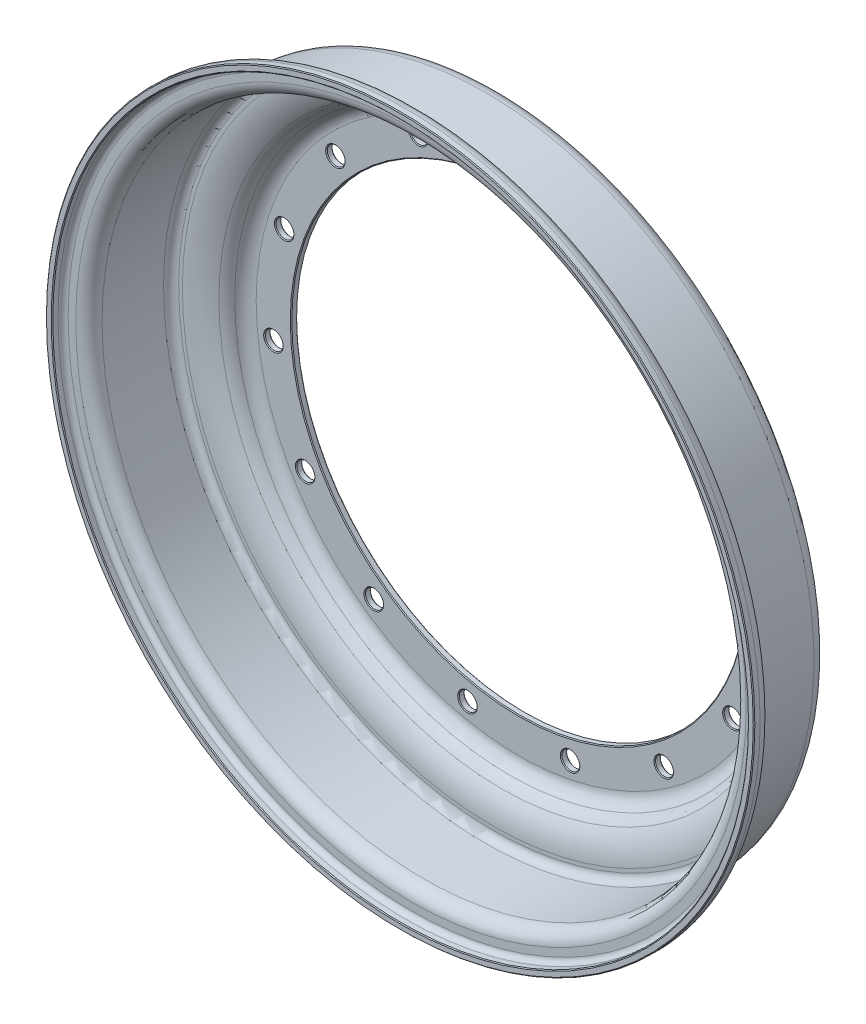
SolidWorks part; units mm, degrees
material "6061-T6 (SS)"
ref_plane "Front Plane" through (0, 0, 0) normal (0, 0, 1) x (1, 0, 0)
ref_plane "Top Plane" through (0, 0, 0) normal (0, 1, 0) x (1, 0, 0)
ref_plane "Right Plane" through (0, 0, 0) normal (1, 0, 0) x (0, 0, -1)
ref_axis "Axis1" through (0, 0, -1.8731) along (0, 0, 1)
sketch "Sketch1" plane through (0, 0, 0) normal (1, 0, 0) x (0, 0, -1)
  line L0 (0, 114.3) -> (0, 131.8108)
  line L1 (-12.8246, 156.0362) -> (-12.8246, 157.8624)
  line L2 (-19.8095, 164.8473) -> (-50.6705, 164.8473)
  line L3 (-54.0991, 168.2759) -> (-54.0991, 172.0859)
  line L4 (-59.8142, 177.801) -> (-62.8622, 177.801)
  line L5 (-3.175, 114.3) -> (-3.175, 131.8108)
  line L6 (-15.9996, 156.0362) -> (-15.9996, 157.8624)
  line L7 (-19.8095, 161.6723) -> (-50.6705, 161.6723)
  line L8 (-57.2741, 168.2759) -> (-57.2741, 172.0859)
  line L9 (-59.8142, 174.626) -> (-62.8622, 174.626)
  line L10 (-62.8622, 177.801) -> (-62.8622, 174.626)
  line L11 (-3.175, 114.3) -> (0, 114.3)
  arc A0 (0, 131.8108) -> (-6.2586, 141.1935) centre (-10.1625, 131.8108) ccw
  arc A1 (-6.2586, 141.1935) -> (-9.1491, 143.604) centre (-3.8185, 147.0578) cw
  arc A2 (-9.1491, 143.604) -> (-12.8246, 156.0362) centre (10.0384, 156.0362) cw
  arc A3 (-12.8246, 157.8624) -> (-19.8095, 164.8473) centre (-19.8095, 157.8624) ccw
  arc A4 (-50.6705, 164.8473) -> (-54.0991, 168.2759) centre (-50.6705, 168.2759) cw
  arc A5 (-54.0991, 172.0859) -> (-59.8142, 177.801) centre (-59.8142, 172.0859) ccw
  arc A6 (-3.175, 131.8108) -> (-7.4782, 138.2621) centre (-10.1625, 131.8108) ccw
  arc A7 (-7.4782, 138.2621) -> (-11.8137, 141.8775) centre (-3.8185, 147.0578) cw
  arc A8 (-11.8137, 141.8775) -> (-15.9996, 156.0362) centre (10.0384, 156.0362) cw
  arc A9 (-15.9996, 157.8624) -> (-19.8095, 161.6723) centre (-19.8095, 157.8624) ccw
  arc A10 (-50.6705, 161.6723) -> (-57.2741, 168.2759) centre (-50.6705, 168.2759) cw
  arc A11 (-57.2741, 172.0859) -> (-59.8142, 174.626) centre (-59.8142, 172.0859) ccw
  dimension "D1" = 114.3
  dimension "D2" = 17.5108
  dimension "D3" = 9.3828
  dimension "D4" = 2.8905
  dimension "D5" = 6.2586
  dimension "D6" = 2.4105
  dimension "D7" = 1.8263
  dimension "D8" = 12.9642
  dimension "D9" = 9.8781
  dimension "D10" = 30.861
  dimension "D11" = 4.8489
  dimension "D12" = 3.81
  dimension "D13" = 8.0823
  dimension "D14" = 3.048
  dimension "D15" = 3.175
revolve "Inner Rim" add sketch "Sketch1" angle 360 about axis through (0, 0, -1.8731) along (0, 0, 1)
sketch "Sketch2" plane through (0, 0, 3.175) normal (0, 0, 1) x (1, 0, 0)
  circle A0 centre (0, 123.825) radius 4.4983
  circle A1 centre (0, 0) radius 114.3 construction
  dimension "D2" = 8.9967
  dimension "D1" = 9.525
extrude "Mounting Hole" cut sketch "Sketch2" against normal through all
pattern_circular "Mounting Hole Pattern" count 15 over 360 about axis through (0, 0, 0) along (0, 0, 1) of "Mounting Hole"
chamfer "Edge Chamfer" distance 0.3962 angle 45 34 edges at (-114.3, 0, 0) (4.4983, 123.825, 0) (-46.2547, 114.9494, 0) (-89.0099, 86.198, 0) (-116.3745, 42.5422, 0) (-123.6169, -8.4695, 0) (-109.4848, -58.0168, 0) (-76.4217, -97.5325, 0) (-30.1447, -120.1839, 0) (21.3446, -122.0544, 0) (69.1433, -102.8206, 0) (104.9864, -65.8082, 0) (122.6765, -17.4169, 0) (119.1546, 33.9859, 0) (95.0299, 79.5122, 0) (54.4736, 111.2901, 0) (-114.3, 0, 3.175) (4.4983, 123.825, 3.175) (-46.2547, 114.9494, 3.175) (-89.0099, 86.198, 3.175) (-116.3745, 42.5422, 3.175) (-123.6169, -8.4695, 3.175) (-109.4848, -58.0168, 3.175) (-76.4217, -97.5325, 3.175) (-30.1447, -120.1839, 3.175) (21.3446, -122.0544, 3.175) (69.1433, -102.8206, 3.175) (104.9864, -65.8082, 3.175) (122.6765, -17.4169, 3.175) (119.1546, 33.9859, 3.175) (95.0299, 79.5122, 3.175) (54.4736, 111.2901, 3.175) (-177.801, 0, 62.8622) (-174.626, 0, 62.8622)
